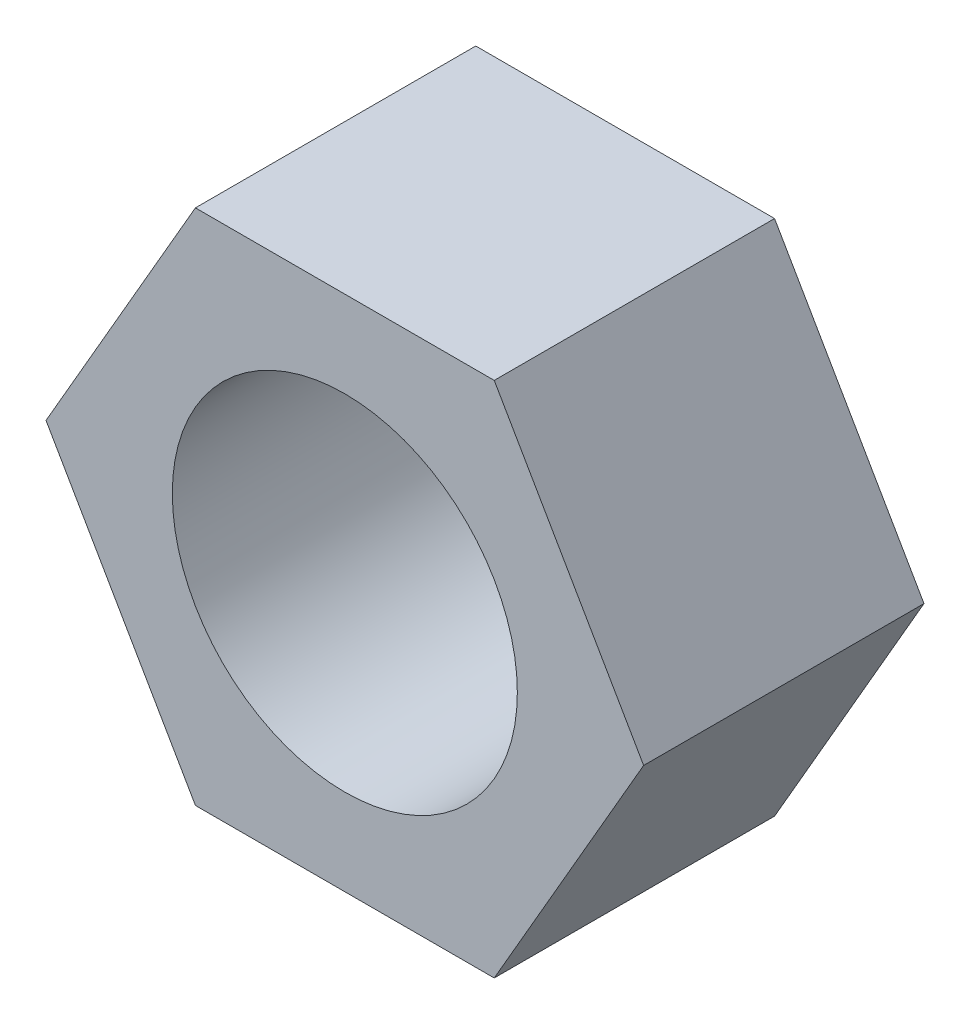
SolidWorks part; units mm, degrees
material "1.4000 (X6Cr13)"
ref_plane "Plano frontal" through (0, 0, 0) normal (0, 0, 1) x (1, 0, 0)
ref_plane "Plano superior" through (0, 0, 0) normal (0, 1, 0) x (1, 0, 0)
ref_plane "Plano direito" through (0, 0, 0) normal (1, 0, 0) x (0, 0, -1)
sketch "Esboço1" plane through (0, 0, 0) normal (0, 0, 1) x (1, 0, 0)
  line L1 (6.9282, 0) -> (3.4641, 6)
  line L2 (3.4641, 6) -> (-3.4641, 6)
  line L3 (-3.4641, 6) -> (-6.9282, 0)
  line L4 (-6.9282, 0) -> (-3.4641, -6)
  line L5 (-3.4641, -6) -> (3.4641, -6)
  line L6 (3.4641, -6) -> (6.9282, 0)
  circle A0 centre (0, 0) radius 4
  circle A1 centre (0, 0) radius 6 construction
  dimension "D1" = 12
  dimension "D2" = 8
extrude "Ressalto-extrusão1" add sketch "Esboço1" along normal blind 6.5
